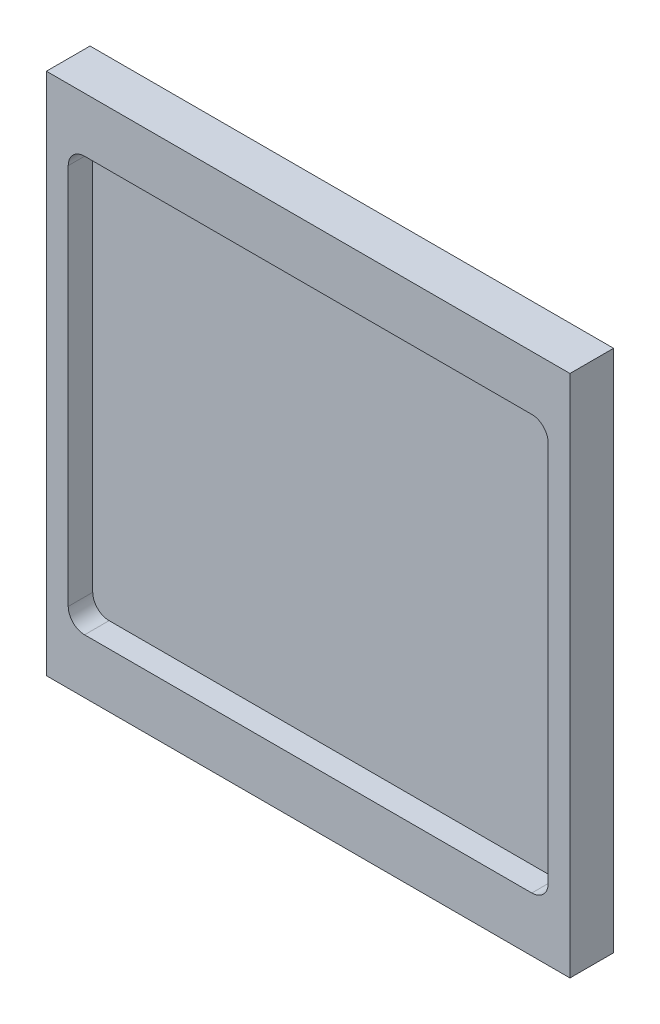
SolidWorks part; units mm, degrees
material "6061-T6 (SS)"
ref_plane "Front Plane" through (0, 0, 0) normal (0, 0, 1) x (1, 0, 0)
ref_plane "Top Plane" through (0, 0, 0) normal (0, 1, 0) x (1, 0, 0)
ref_plane "Right Plane" through (0, 0, 0) normal (1, 0, 0) x (0, 0, -1)
sketch "Sketch1" plane through (0, 0, 0) normal (0, 0, 1) x (1, 0, 0)
  line L1 (-76.2, 76.2) -> (76.2, 76.2)
  line L2 (-76.2, 76.2) -> (-76.2, -76.2)
  line L3 (-76.2, -76.2) -> (76.2, -76.2)
  line L4 (76.2, 76.2) -> (76.2, -76.2)
  line L5 (-76.2, 76.2) -> (76.2, -76.2) construction
  line L6 (-76.2, -76.2) -> (76.2, 76.2) construction
  point P0 (0, 0)
  dimension "D1" = 152.4
  dimension "D2" = 152.4
extrude "Boss-Extrude1" add sketch "Sketch1" along normal blind 12.7
sketch "Sketch2" plane through (0, 0, 12.7) normal (0, 0, 1) x (1, 0, 0)
  line L0 (76.2, -76.2) -> (76.2, 76.2) construction
  line L1 (-65.0875, 60.325) -> (65.0875, 60.325)
  line L2 (-69.85, 55.5625) -> (-69.85, -55.5625)
  line L3 (-65.0875, -60.325) -> (65.0875, -60.325)
  line L4 (69.85, 55.5625) -> (69.85, -55.5625)
  line L5 (-69.85, 60.325) -> (69.85, -60.325) construction
  line L6 (-69.85, -60.325) -> (69.85, 60.325) construction
  line L7 (76.2, 76.2) -> (-76.2, 76.2) construction
  arc A0 (-69.85, -55.5625) -> (-65.0875, -60.325) centre (-65.0875, -55.5625) ccw
  arc A1 (65.0875, -60.325) -> (69.85, -55.5625) centre (65.0875, -55.5625) ccw
  arc A2 (65.0875, 60.325) -> (69.85, 55.5625) centre (65.0875, 55.5625) cw
  arc A3 (-65.0875, 60.325) -> (-69.85, 55.5625) centre (-65.0875, 55.5625) ccw
  point P0 (0, 0)
  dimension "D3" = 4.7625
  dimension "D1" = 6.35
  dimension "D2" = 15.875
extrude "Cut-Extrude1" cut sketch "Sketch2" against normal blind 7.1374
